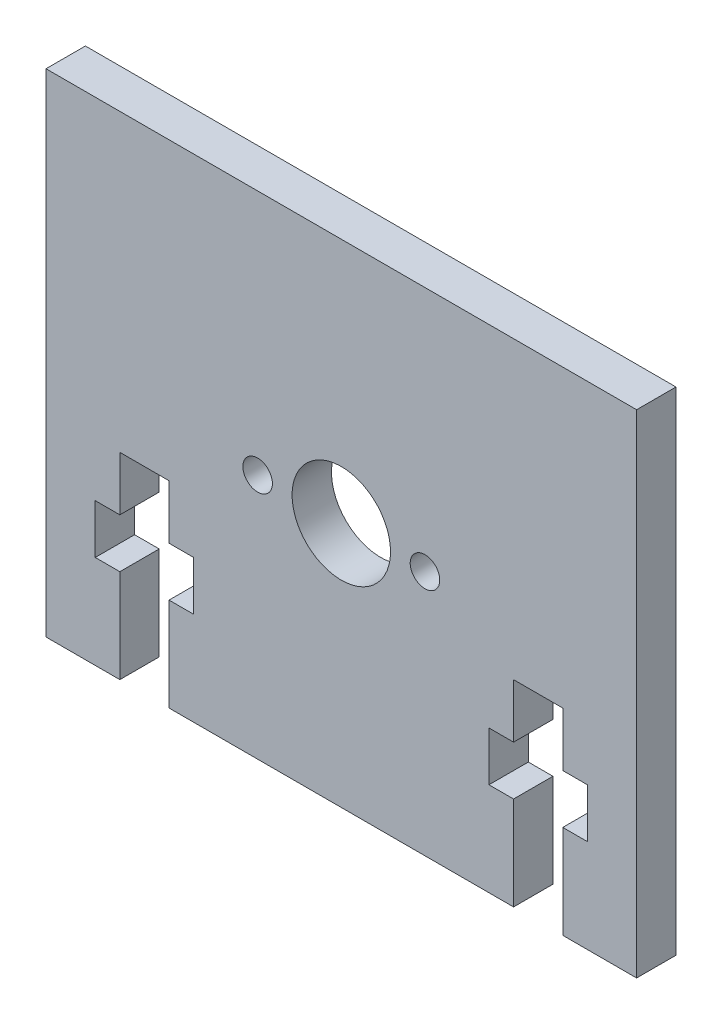
SolidWorks part; units mm, degrees
material "Pine"
ref_plane "Front Plane" through (0, 0, 0) normal (0, 0, 1) x (1, 0, 0)
ref_plane "Top Plane" through (0, 0, 0) normal (0, 1, 0) x (1, 0, 0)
ref_plane "Right Plane" through (0, 0, 0) normal (1, 0, 0) x (0, 0, -1)
sketch "Sketch1" plane through (0, 0, 0) normal (0, 0, 1) x (1, 0, 0)
  line L0 (0, -25) -> (0, 25) construction
  line L1 (30, 25) -> (-30, 25)
  line L2 (30, 25) -> (30, -25)
  line L3 (30, -25) -> (-30, -25)
  line L4 (-30, 25) -> (-30, -25)
  line L5 (30, 25) -> (-30, -25) construction
  line L6 (30, -25) -> (-30, 25) construction
  circle A0 centre (0, 0) radius 5
  circle A1 centre (-8.5, 0) radius 1.5
  circle A2 centre (8.5, 0) radius 1.5
  point P0 (0, 0)
  dimension "D1" = 50
  dimension "D3" = 10
  dimension "D5" = 3
  dimension "D2" = 17
  dimension "D4" = 8.5
  dimension "D6" = 60
extrude "Boss-Extrude1" add sketch "Sketch1" along normal blind 4
sketch "Sketch2" plane through (0, 0, 4) normal (0, 0, 1) x (1, 0, 0)
  line L0 (-20, -25) -> (-20, 2.0451) construction
  line L1 (-30, -25) -> (30, -25) construction
  line L2 (20, -25) -> (20, 2.0451) construction
  line L3 (-30, 25) -> (-30, -25) construction
  line L4 (30, -25) -> (30, 25) construction
  line L5 (-30, -25) -> (30, -25) construction
  line L6 (-17.5, -5) -> (-22.5, -5)
  line L7 (-17.5, -5) -> (-17.5, -10.5)
  line L8 (-17.5, -25) -> (-22.5, -25)
  line L9 (-22.5, -5) -> (-22.5, -10.5)
  line L10 (-17.5, -5) -> (-22.5, -25) construction
  line L11 (-17.5, -25) -> (-22.5, -5) construction
  line L12 (22.5, -5) -> (17.5, -5)
  line L13 (22.5, -5) -> (22.5, -10.5)
  line L14 (22.5, -25) -> (17.5, -25)
  line L15 (17.5, -5) -> (17.5, -10.5)
  line L16 (22.5, -5) -> (17.5, -25) construction
  line L17 (22.5, -25) -> (17.5, -5) construction
  line L18 (-15, -10.5) -> (-17.5, -10.5)
  line L19 (-15, -10.5) -> (-15, -15.5)
  line L20 (-15, -15.5) -> (-17.5, -15.5)
  line L21 (-25, -10.5) -> (-25, -15.5)
  line L22 (-15, -10.5) -> (-25, -15.5) construction
  line L23 (-15, -15.5) -> (-25, -10.5) construction
  line L24 (25, -15.5) -> (22.5, -15.5)
  line L25 (25, -15.5) -> (25, -10.5)
  line L26 (25, -10.5) -> (22.5, -10.5)
  line L27 (15, -15.5) -> (15, -10.5)
  line L28 (25, -15.5) -> (15, -10.5) construction
  line L29 (25, -10.5) -> (15, -15.5) construction
  line L30 (-22.5, -10.5) -> (-25, -10.5)
  line L31 (-17.5, -15.5) -> (-17.5, -25)
  line L32 (-22.5, -15.5) -> (-25, -15.5)
  line L33 (-22.5, -15.5) -> (-22.5, -25)
  line L34 (17.5, -10.5) -> (15, -10.5)
  line L35 (17.5, -15.5) -> (17.5, -25)
  line L36 (17.5, -15.5) -> (15, -15.5)
  line L38 (22.5, -15.5) -> (22.5, -25)
  point P10 (-20, -15)
  point P15 (20, -15)
  point P20 (-20, -13)
  point P25 (20, -13)
  dimension "D1" = 10
  dimension "D2" = 10
  dimension "D3" = 20
  dimension "D4" = 5
  dimension "D5" = 5
  dimension "D6" = 10
  dimension "D7" = 12
  dimension "D8" = 12
  dimension "D9" = 20
  dimension "D10" = 10
extrude "Cut-Extrude1" cut sketch "Sketch2" against normal through all
